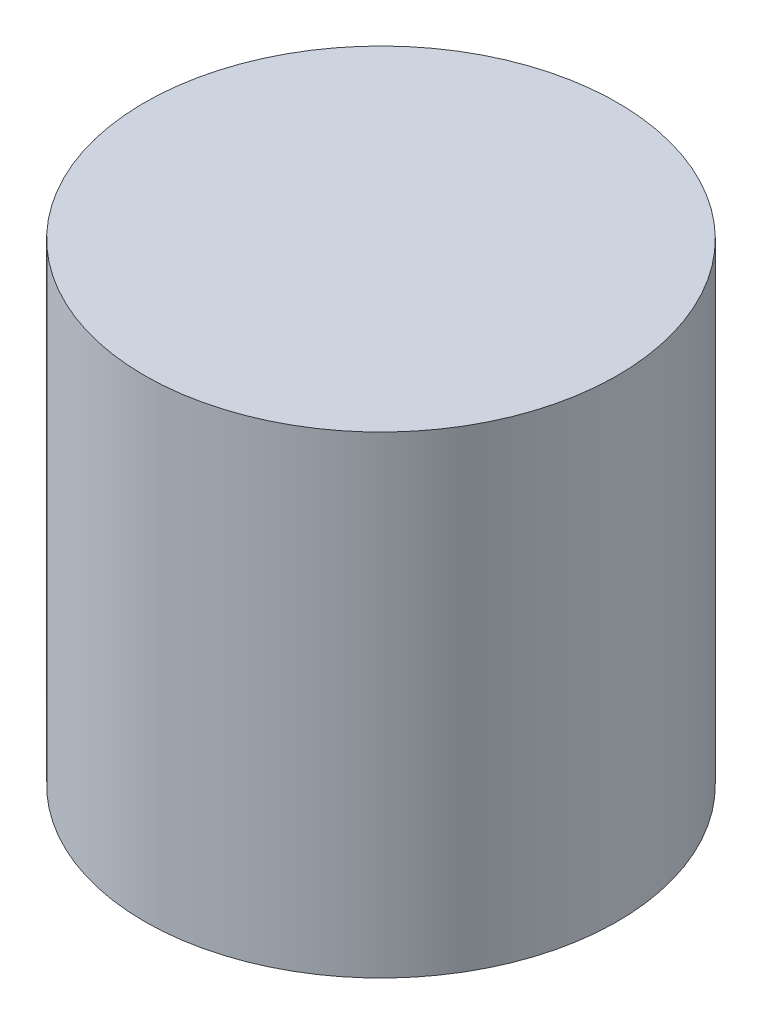
SolidWorks part; units mm, degrees
material "Ductile Iron"
ref_plane "Front Plane" through (0, 0, 0) normal (0, 0, 1) x (1, 0, 0)
ref_plane "Top Plane" through (0, 0, 0) normal (0, 1, 0) x (1, 0, 0)
ref_plane "Right Plane" through (0, 0, 0) normal (1, 0, 0) x (0, 0, -1)
sketch "Sketch1" plane through (0, 0, 0) normal (0, 1, 0) x (1, 0, 0)
  circle A0 centre (0, 0) radius 2.3812
  dimension "D1" = 4.7625
extrude "Boss-Extrude1" add sketch "Sketch1" along normal mid plane 4.7625
